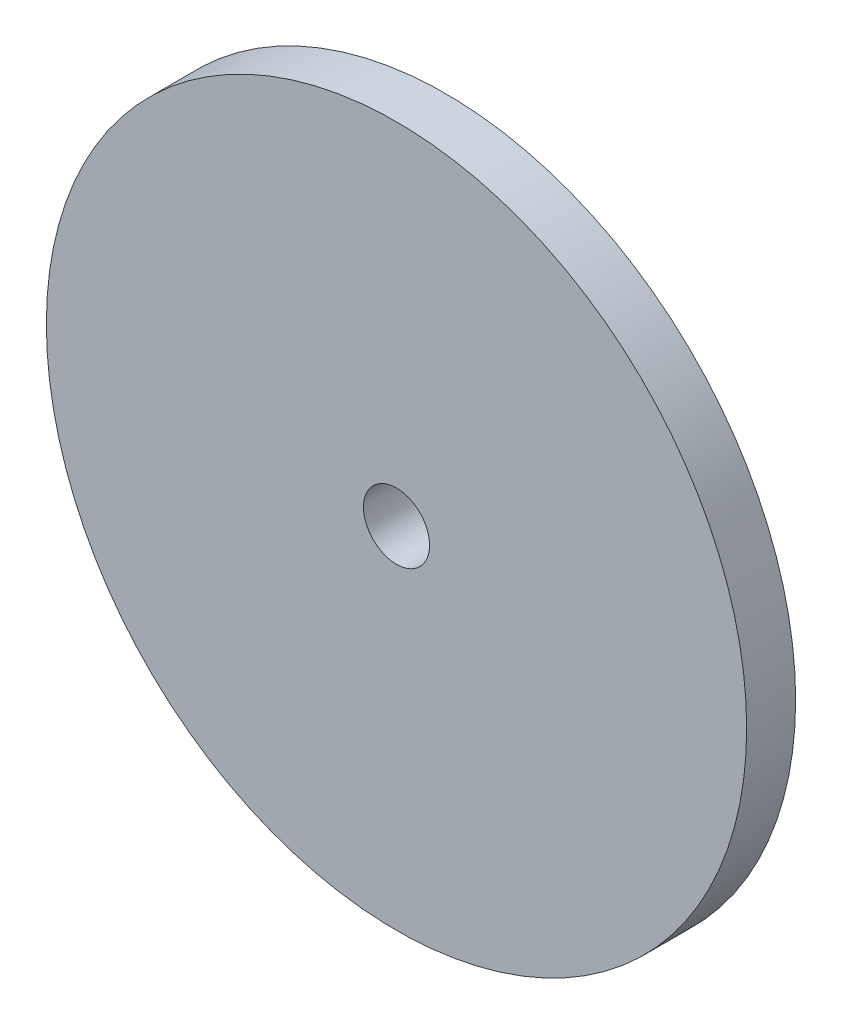
SolidWorks part; units mm, degrees
ref_plane "Plan de face" through (0, 0, 0) normal (0, 0, 1) x (1, 0, 0)
ref_plane "Plan de dessus" through (0, 0, 0) normal (0, 1, 0) x (1, 0, 0)
ref_plane "Plan de droite" through (0, 0, 0) normal (1, 0, 0) x (0, 0, -1)
sketch "Esquisse1" plane through (0, 0, 0) normal (0, 0, 1) x (1, 0, 0)
  circle A0 centre (0, 0) radius 14.3
  circle A1 centre (0, 0) radius 1.35
extrude "Boss.-Extru.3" add sketch "Esquisse1" along normal blind 2 contours A0
